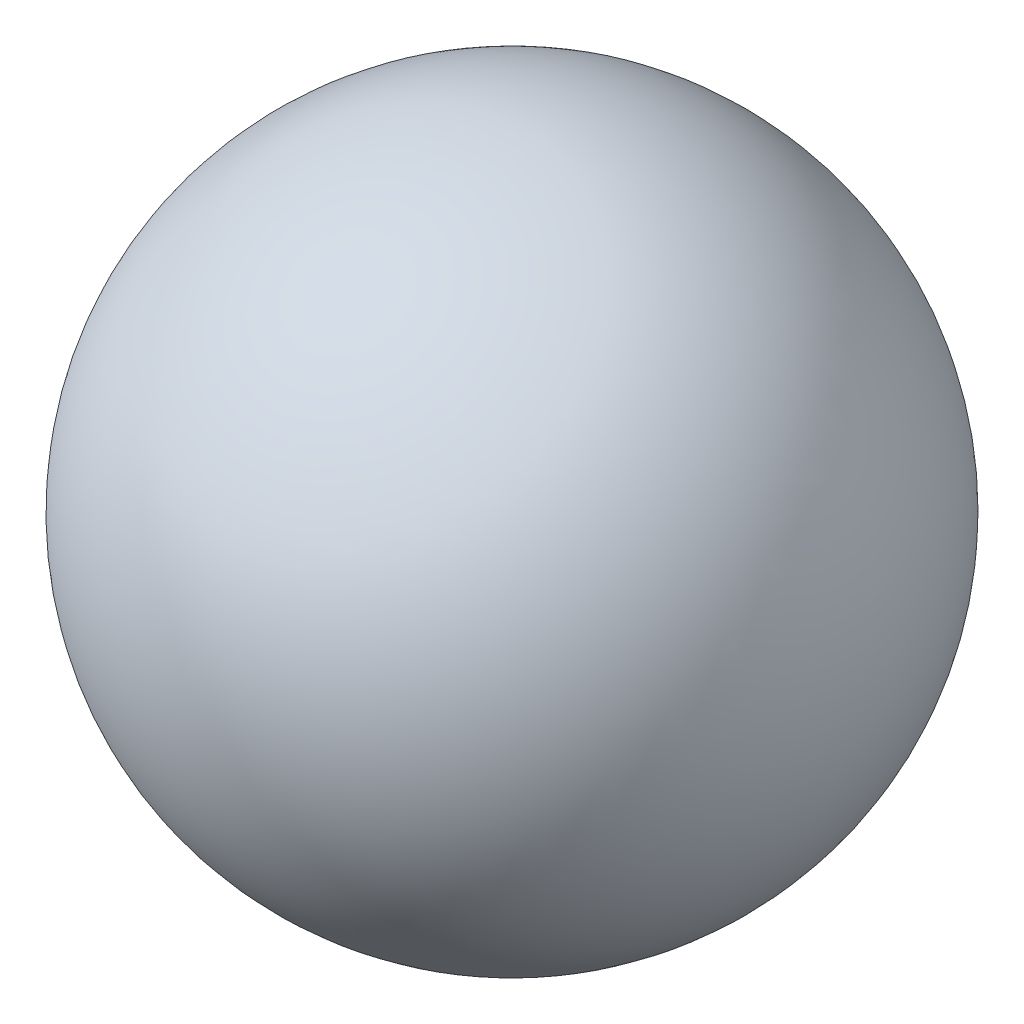
SolidWorks part; units mm, degrees
ref_plane "Front Plane" through (0, 0, 0) normal (0, 0, 1) x (1, 0, 0)
ref_plane "Top Plane" through (0, 0, 0) normal (0, 1, 0) x (1, 0, 0)
ref_plane "Right Plane" through (0, 0, 0) normal (1, 0, 0) x (0, 0, -1)
sketch "Sketch1" plane through (0, 0, 0) normal (0, 0, 1) x (1, 0, 0)
  line L0 (0, 5) -> (0, -5) construction
  circle A0 centre (0, 0) radius 5
  dimension "D1" = 10
revolve "Revolve2" add sketch "Sketch1" angle 360 about L0
sketch "Sketch2" plane through (0, 0, 0) normal (0, 1, 0) x (1, 0, 0)
  circle A0 centre (0, 0) radius 2
  dimension "D1" = 4
extrude "Cut-Extrude1" cut sketch "Sketch2" against normal through all
